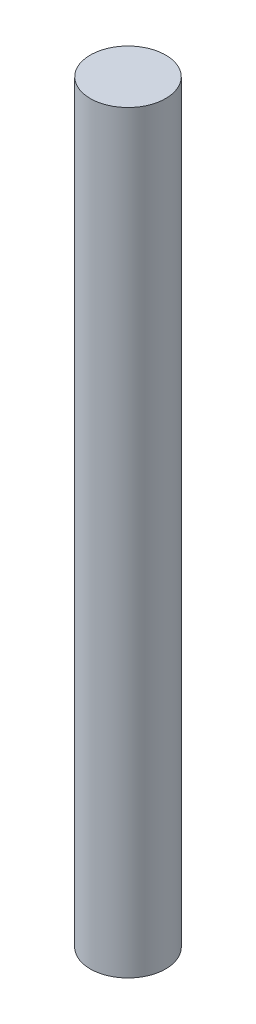
SolidWorks part; units mm, degrees
ref_plane "Front Plane" through (0, 0, 0) normal (0, 0, 1) x (1, 0, 0)
ref_plane "Top Plane" through (0, 0, 0) normal (0, 1, 0) x (1, 0, 0)
ref_plane "Right Plane" through (0, 0, 0) normal (1, 0, 0) x (0, 0, -1)
sketch "Sketch1" plane through (0, 0, 0) normal (0, 1, 0) x (1, 0, 0)
  circle A0 centre (0, 0) radius 1.5
  dimension "D1" = 3
extrude "Boss-Extrude1" add sketch "Sketch1" along normal blind 30
